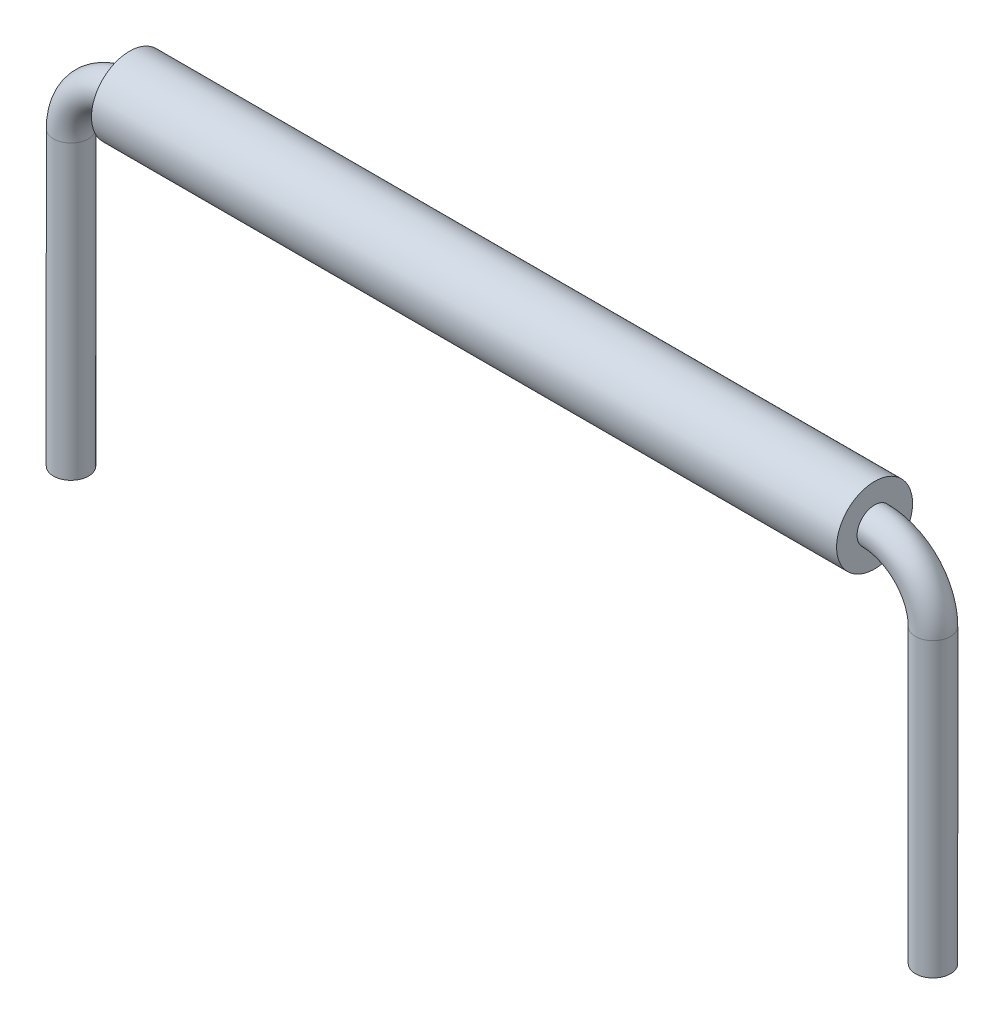
SolidWorks part; units mm, degrees
other "Wire"
other "Insulation"
ref_plane "Front Plane" through (0, 0, 0) normal (0, 0, 1) x (1, 0, 0)
ref_plane "Top Plane" through (0, 0, 0) normal (0, 1, 0) x (1, 0, 0)
ref_plane "Right Plane" through (0, 0, 0) normal (1, 0, 0) x (0, 0, -1)
sketch "Sketch1" plane through (0, 0, 0) normal (0, 0, 1) x (1, 0, 0)
  line L0 (-6.3775, 0) -> (6.3775, 0)
  line L1 (-7.3775, -1) -> (-7.3775, -6)
  line L2 (7.3775, -1) -> (7.3775, -6)
  line L3 (0, 0) -> (0, -6) construction
  line L4 (-7.3775, -6) -> (7.3775, -6) construction
  arc A0 (-6.3775, 0) -> (-7.3775, -1) centre (-6.3775, -1) ccw
  arc A1 (6.3775, 0) -> (7.3775, -1) centre (6.3775, -1) cw
  dimension "D1" = 1
  dimension "D2" = 14.755
  dimension "D3" = 6
sketch "Sketch2" plane through (0, 0, 0) normal (1, 0, 0) x (0, 0, -1)
  circle A0 centre (0, 0) radius 0.3
  dimension "D1" = 0.6
sweep "Sweep1" add profiles "Sketch2" path "Sketch1"
sketch "Sketch3" plane through (0, 0, 0) normal (1, 0, 0) x (0, 0, -1)
  circle A0 centre (0, 0) radius 0.65
  circle A1 centre (0, 0) radius 0.3
  dimension "D1" = 1.3
  dimension "D2" = 0.6
extrude "Boss-Extrude1" add sketch "Sketch3" along normal up to vertex (6.3775 mm away) and the other way up to vertex (6.3775 mm away) separate body up to point (6.3775, 0, 0) other way up to point (-6.3775, 0, 0)
